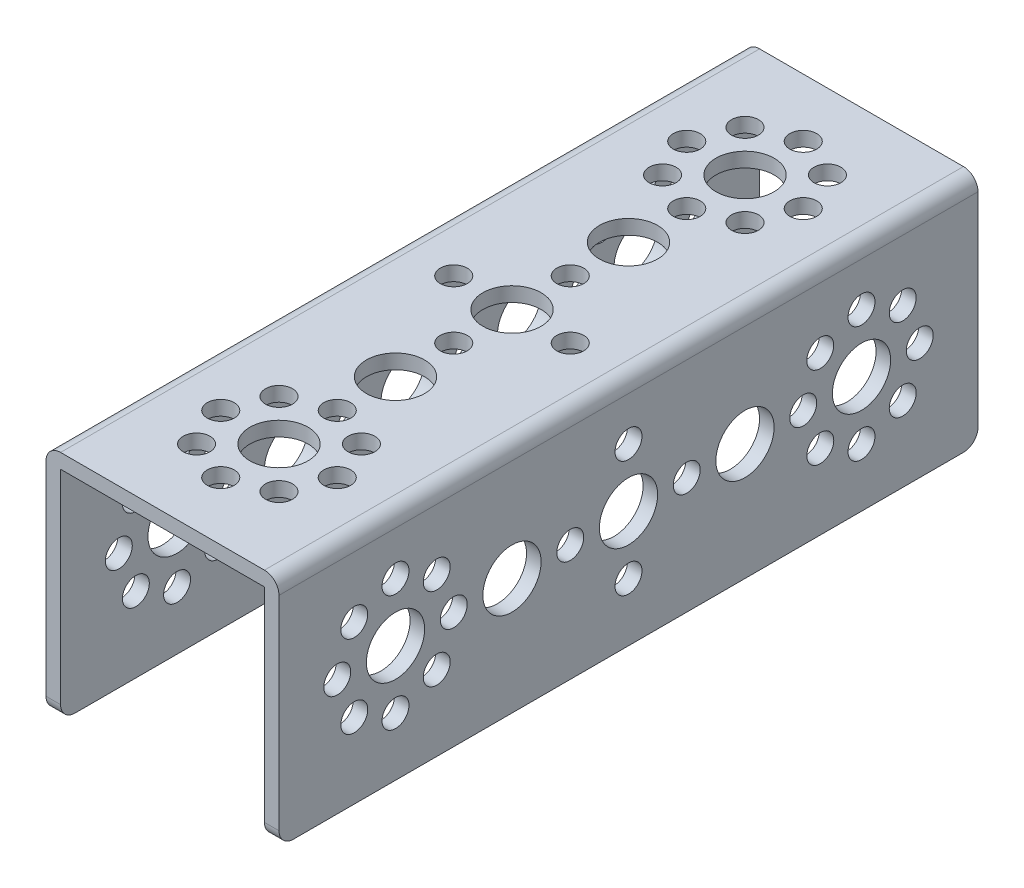
SolidWorks part; units mm, degrees
ref_plane "Front Plane" through (0, 0, 0) normal (0, 0, 1) x (1, 0, 0)
ref_plane "Top Plane" through (0, 0, 0) normal (0, 1, 0) x (1, 0, 0)
ref_plane "Right Plane" through (0, 0, 0) normal (1, 0, 0) x (0, 0, -1)
sketch "Sketch1" plane through (0, 0, 0) normal (0, 0, 1) x (1, 0, 0)
  line L0 (14, -16) -> (16, -16)
  line L1 (-16, 16) -> (16, 16)
  line L2 (-16, 16) -> (-16, -16)
  line L3 (-16, -16) -> (-14, -16)
  line L4 (16, 16) -> (16, -16)
  line L5 (-16, 16) -> (16, -16) construction
  line L6 (-16, -16) -> (16, 16) construction
  line L7 (-14, 14) -> (14, 14)
  line L8 (-14, 14) -> (-14, -16)
  line L10 (14, 14) -> (14, -16)
  point P0 (0, 0)
  dimension "D1" = 32
  dimension "D2" = 32
  dimension "D3" = 2
  dimension "D4" = 2
extrude "Boss-Extrude1" add sketch "Sketch1" against normal blind 96
sketch "Sketch2" plane through (0, 16, 0) normal (0, 1, 0) x (1, 0, 0)
  line L0 (0, 0) -> (0, 165.6972) construction
  line L1 (16, 0) -> (-16, 0) construction
  line L2 (-24.3046, 48) -> (48.8216, 48) construction
  circle B0 centre (0, 32) radius 4
  circle B1 centre (0, 64) radius 4
  circle B2 centre (0, 48) radius 4
  circle B3 centre (0, 56) radius 1.85
  circle B4 centre (0, 40) radius 1.85
  circle B5 centre (8, 48) radius 1.85
  circle B6 centre (-8, 48) radius 1.85
  circle B7 centre (0, 24) radius 1.85
  circle B8 centre (8, 16) radius 1.85
  circle B9 centre (0, 16) radius 4
  circle B10 centre (-8, 16) radius 1.85
  circle B11 centre (-5.66, 10.34) radius 1.85
  circle B12 centre (5.66, 10.34) radius 1.85
  circle B13 centre (0, 8) radius 1.85
  circle B14 centre (-5.66, 21.66) radius 1.85
  circle B15 centre (5.66, 21.66) radius 1.85
  circle B16 centre (0, 88) radius 1.85
  circle B17 centre (8, 80) radius 1.85
  circle B18 centre (0, 80) radius 4
  circle B19 centre (-8, 80) radius 1.85
  circle B20 centre (-5.66, 74.34) radius 1.85
  circle B21 centre (5.66, 74.34) radius 1.85
  circle B22 centre (0, 72) radius 1.85
  circle B23 centre (-5.66, 85.66) radius 1.85
  circle B24 centre (5.66, 85.66) radius 1.85
sketch_block_instance "TETRIX 96 Pattern-1"
sketch_block "TETRIX 96 Pattern" parameters "D1"=16, "D2"=16, "D3"=16, "D4"=16
extrude "Cut-Extrude1" cut sketch "Sketch2" against normal through all
sketch "Sketch3" plane through (16, 0, 0) normal (1, 0, 0) x (0, 0, -1)
  line L0 (-3.4954, 0) -> (176.3323, 0) construction
  line L1 (48, 19.8146) -> (48, -35.1227) construction
  circle B0 centre (64, 0) radius 4
  circle B1 centre (32, 0) radius 4
  circle B2 centre (48, 0) radius 4
  circle B3 centre (40, 0) radius 1.85
  circle B4 centre (56, 0) radius 1.85
  circle B5 centre (48, 8) radius 1.85
  circle B6 centre (48, -8) radius 1.85
  circle B7 centre (72, 0) radius 1.85
  circle B8 centre (80, 8) radius 1.85
  circle B9 centre (80, 0) radius 4
  circle B10 centre (80, -8) radius 1.85
  circle B11 centre (85.66, -5.66) radius 1.85
  circle B12 centre (85.66, 5.66) radius 1.85
  circle B13 centre (88, 0) radius 1.85
  circle B14 centre (74.34, -5.66) radius 1.85
  circle B15 centre (74.34, 5.66) radius 1.85
  circle B16 centre (8, 0) radius 1.85
  circle B17 centre (16, 8) radius 1.85
  circle B18 centre (16, 0) radius 4
  circle B19 centre (16, -8) radius 1.85
  circle B20 centre (21.66, -5.66) radius 1.85
  circle B21 centre (21.66, 5.66) radius 1.85
  circle B22 centre (24, 0) radius 1.85
  circle B23 centre (10.34, -5.66) radius 1.85
  circle B24 centre (10.34, 5.66) radius 1.85
sketch_block_instance "TETRIX 96 Pattern-3"
extrude "Cut-Extrude2" cut sketch "Sketch3" against normal through all
fillet "Fillet1" radius 2 6 edges at (-15, -16, -96) (15, -16, -96) (-15, -16, 0) (15, -16, 0) (-16, 16, -48) (16, 16, -48)
